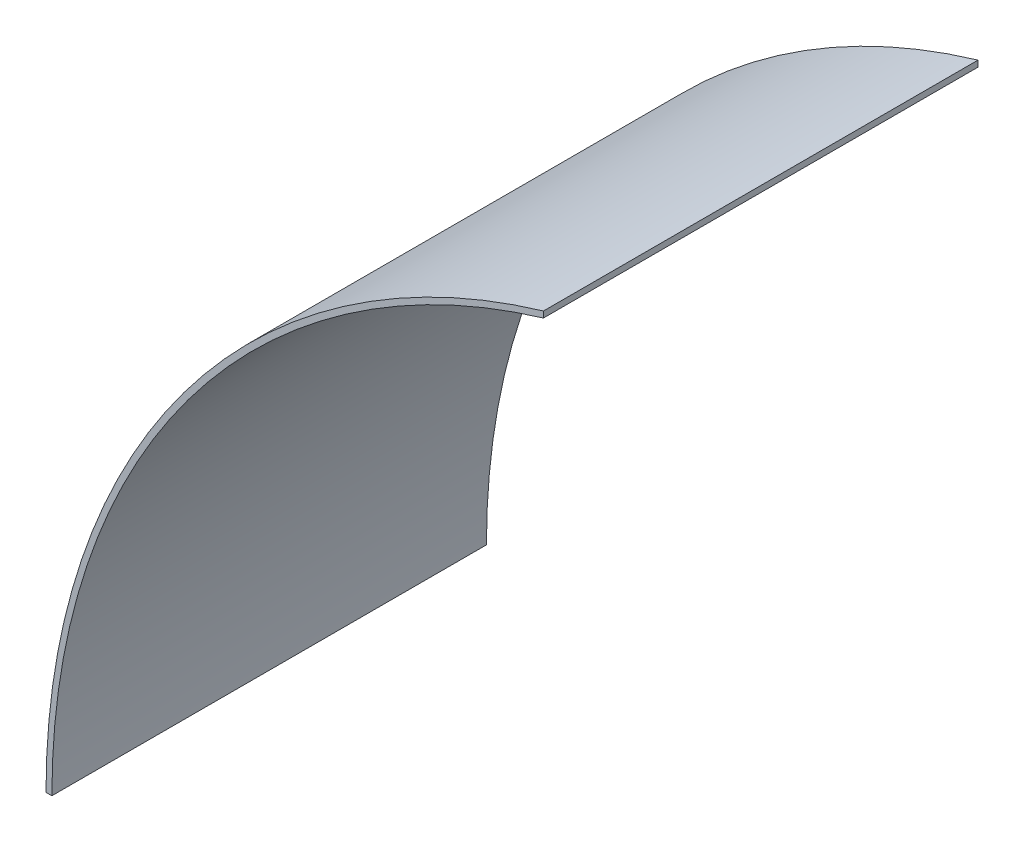
SolidWorks part; units mm, degrees
material "Plain Carbon Steel"
ref_plane "Front Plane" through (0, 0, 0) normal (0, 0, 1) x (1, 0, 0)
ref_plane "Top Plane" through (0, 0, 0) normal (0, 1, 0) x (1, 0, 0)
ref_plane "Right Plane" through (0, 0, 0) normal (1, 0, 0) x (0, 0, -1)
sketch "Sketch1" plane through (0, 0, 0) normal (0, 0, 1) x (1, 0, 0)
  line L0 (0, 0) -> (0, -179.3189) construction
  line L2 (0, 0) -> (101.5936, 0) construction
  line L3 (-50.8, 113.7839) -> (-50.8, -22.985) construction
  line L5 (-50.8, 171.9728) -> (-50.8, 170.3884)
  line L7 (0, 0) -> (-177.8, 0) construction
  line L10 (-53.3, 169.623) -> (-53.3, 171.2144) construction
  line L25 (-179.3189, 0) -> (-177.8, 0)
  circle A0 centre (0, 0) radius 177.8 construction
  circle A1 centre (0, 0) radius 179.3189 construction
  arc A2 (-177.8, 0) -> (-50.8, 170.3884) centre (0, 0) cw
  arc A3 (-179.3189, 0) -> (-50.8, 171.9728) centre (0, 0) cw
  dimension "D1" = 355.6
  dimension "D2" = 358.6378
  dimension "D3" = 50.8
  dimension "D4" = 5
extrude "Inner Ring - Left Side" add sketch "Sketch1" along normal blind 112.268
